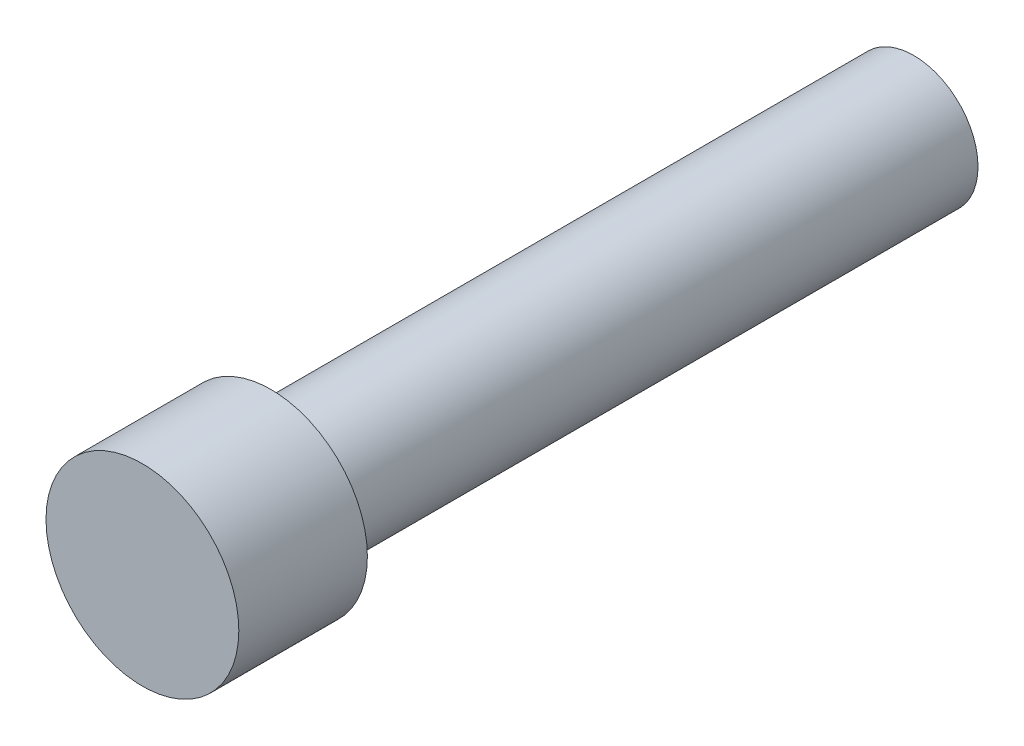
SolidWorks part; units mm, degrees
material "1060 Alloy"
ref_plane "Front Plane" through (0, 0, 0) normal (0, 0, 1) x (1, 0, 0)
ref_plane "Top Plane" through (0, 0, 0) normal (0, 1, 0) x (1, 0, 0)
ref_plane "Right Plane" through (0, 0, 0) normal (1, 0, 0) x (0, 0, -1)
sketch "Sketch1" plane through (0, 0, 0) normal (0, 0, 1) x (1, 0, 0)
  circle A0 centre (0, 0) radius 0.25
  dimension "D1" = 0.5
extrude "Boss-Extrude1" add sketch "Sketch1" along normal blind 2.5
sketch "Sketch2" plane through (0, 0, 2.5) normal (0, 0, 1) x (1, 0, 0)
  circle A0 centre (0, 0) radius 0.375
  dimension "D1" = 0.75
extrude "Boss-Extrude2" add sketch "Sketch2" along normal blind 0.5
